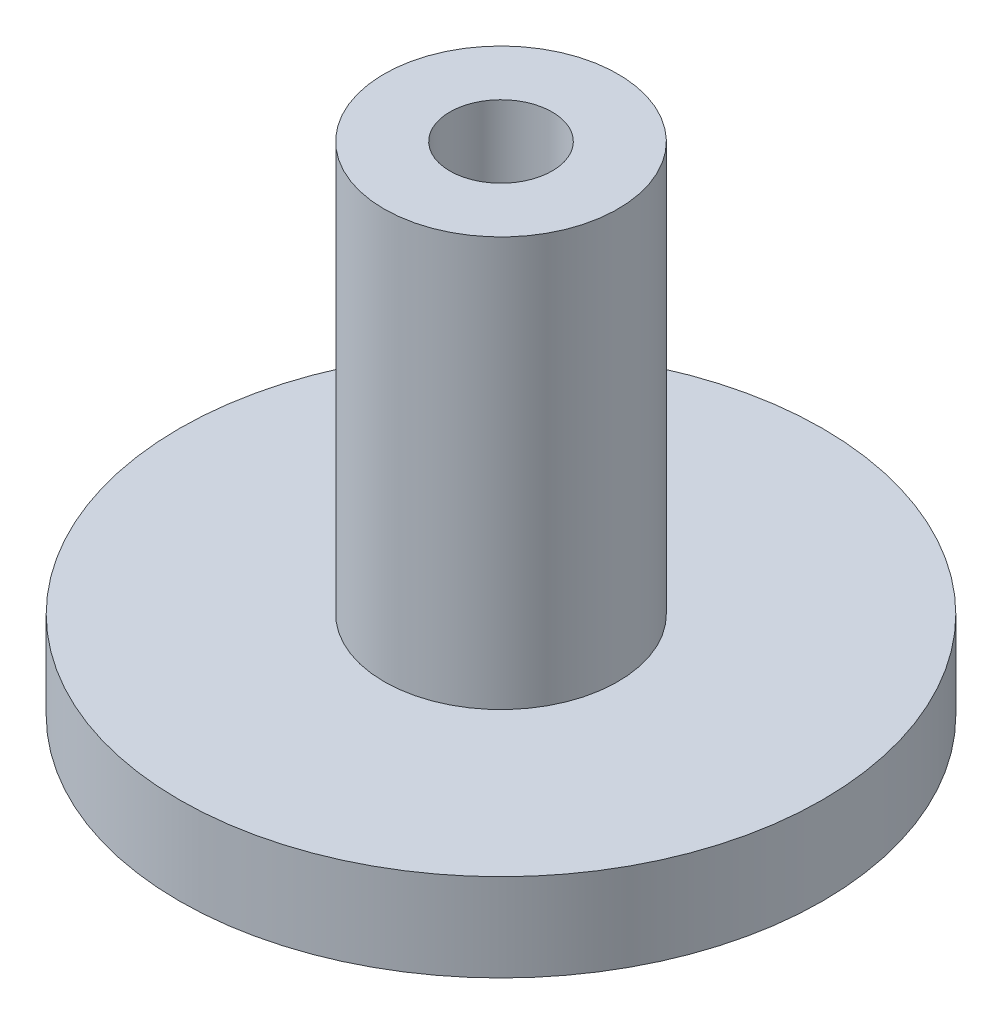
SolidWorks part; units mm, degrees
ref_plane "Front Plane" through (0, 0, 0) normal (0, 0, 1) x (1, 0, 0)
ref_plane "Top Plane" through (0, 0, 0) normal (0, 1, 0) x (1, 0, 0)
ref_plane "Right Plane" through (0, 0, 0) normal (1, 0, 0) x (0, 0, -1)
sketch "Sketch1" plane through (0, 0, 0) normal (0, 1, 0) x (1, 0, 0)
  circle A0 centre (0, 0) radius 11
extrude "Boss-Extrude1" add sketch "Sketch1" along normal blind 3
sketch "Sketch2" plane through (0, 3, 0) normal (0, 1, 0) x (1, 0, 0)
  circle A0 centre (0, 0) radius 4
extrude "Boss-Extrude2" add sketch "Sketch2" along normal blind 14
sketch "Sketch3" plane through (0, 17, 0) normal (0, 1, 0) x (1, 0, 0)
  circle A0 centre (0, 0) radius 1.75
extrude "Cut-Extrude1" cut sketch "Sketch3" against normal blind 20
